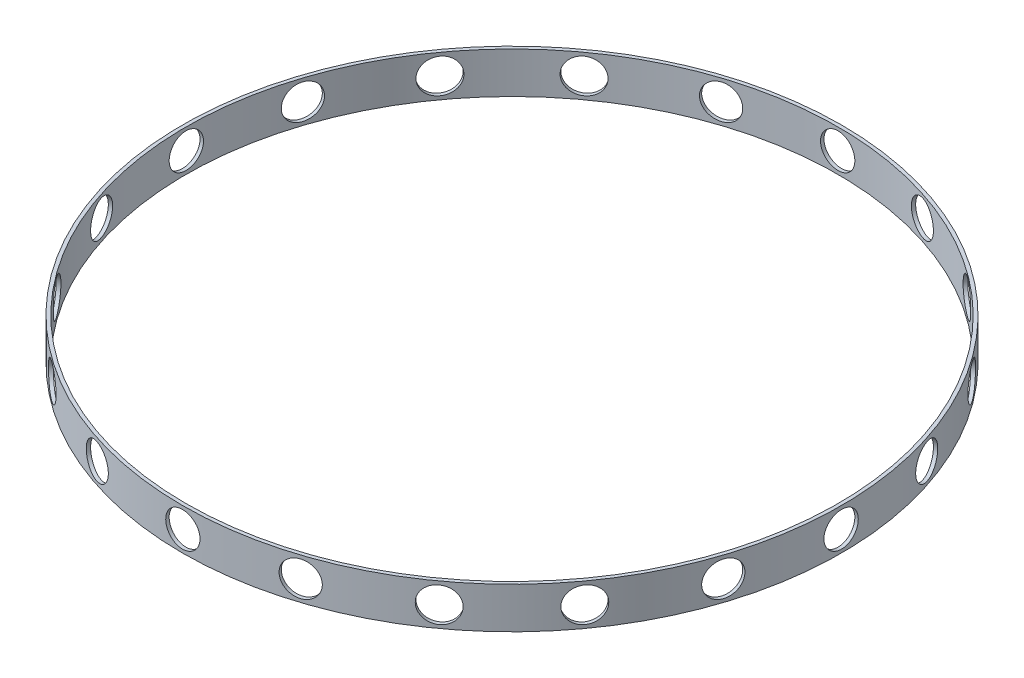
SolidWorks part; units mm, degrees
ref_plane "Front Plane" through (0, 0, 0) normal (0, 0, 1) x (1, 0, 0)
ref_plane "Top Plane" through (0, 0, 0) normal (0, 1, 0) x (1, 0, 0)
ref_plane "Right Plane" through (0, 0, 0) normal (1, 0, 0) x (0, 0, -1)
sketch "Sketch1" plane through (0, 0, 0) normal (0, 1, 0) x (1, 0, 0)
  circle A1 centre (0, 0) radius 47.5
  circle A2 centre (0, 0) radius 48
  dimension "D2" = 95
  dimension "D1" = 96
extrude "Boss-Extrude2" add sketch "Sketch1" along normal blind 6 contours A1 | A2
sketch "Sketch5" plane through (0, 0, 0) normal (0, 0, 1) x (1, 0, 0)
  line L0 (47.5, 6) -> (-47.5, 6) construction
  circle A0 centre (0, 3) radius 2.5
  dimension "D1" = 5
  dimension "D2" = 3
extrude "Cut-Extrude1" cut sketch "Sketch5" against normal through all both and the other way through all
pattern_circular "CirPattern1" count 20 over 360 about axis through (0, 6, 0) along (0, -1, 0) of "Cut-Extrude1"
equation "\"inner_diameter\"= 90mm"
equation "\"D1@Sketch1\"=\"inner_diameter\"+6"
equation "\"D2@Sketch1\"=\"inner_diameter\"+5"
equation "\"D1@CirPattern1\"=20"
